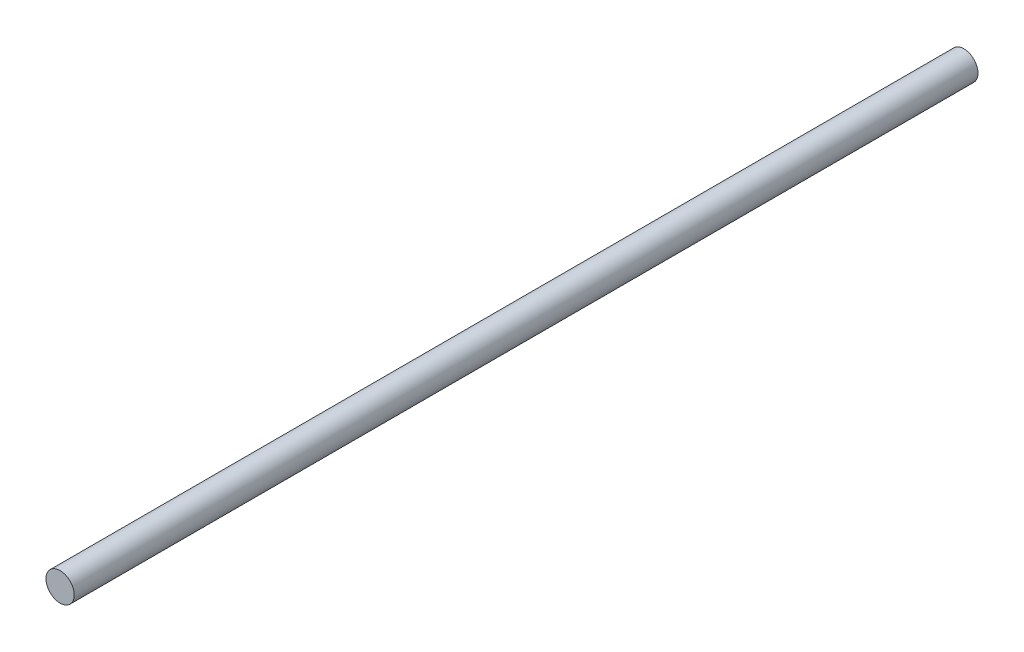
SolidWorks part; units mm, degrees
material "1023 Carbon Steel Sheet (SS)"
ref_plane "Front Plane" through (0, 0, 0) normal (0, 0, 1) x (1, 0, 0)
ref_plane "Top Plane" through (0, 0, 0) normal (0, 1, 0) x (1, 0, 0)
ref_plane "Right Plane" through (0, 0, 0) normal (1, 0, 0) x (0, 0, -1)
sketch "Sketch1" plane through (0, 0, 0) normal (0, 0, 1) x (1, 0, 0)
  circle A0 centre (0, 0) radius 6.35
  dimension "D1" = 12.7
extrude "Boss-Extrude1" add sketch "Sketch1" along normal mid plane 406.4
